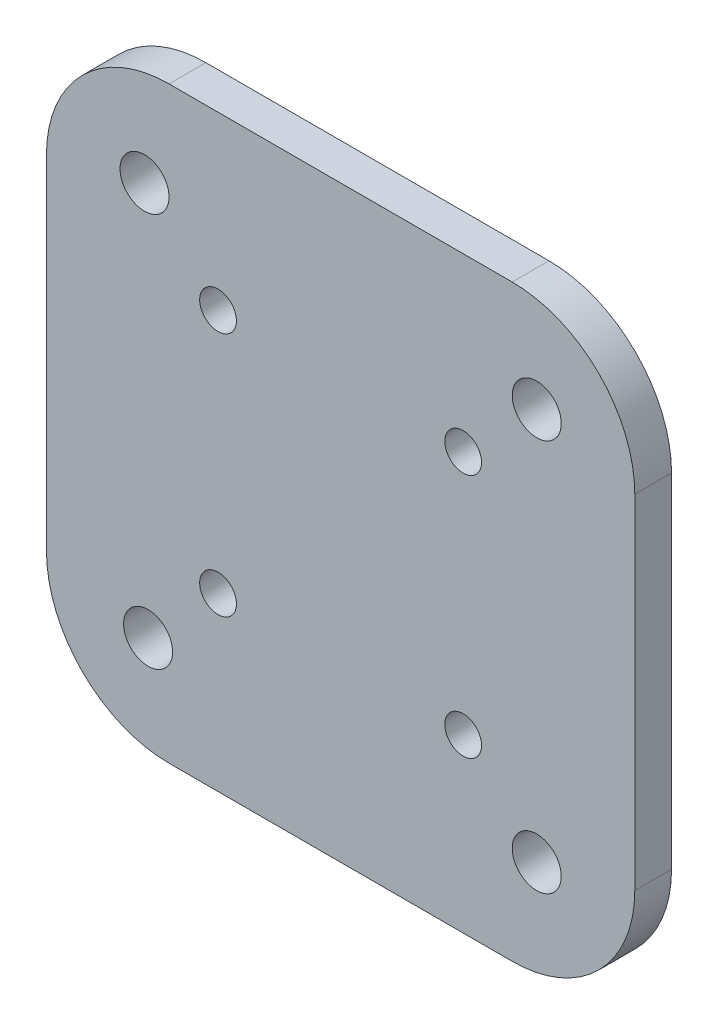
SolidWorks part; units mm, degrees
ref_plane "Front Plane" through (0, 0, 0) normal (0, 0, 1) x (1, 0, 0)
ref_plane "Top Plane" through (0, 0, 0) normal (0, 1, 0) x (1, 0, 0)
ref_plane "Right Plane" through (0, 0, 0) normal (1, 0, 0) x (0, 0, -1)
sketch "Sketch1" plane through (0, 0, 0) normal (0, 0, 1) x (1, 0, 0)
  line L5 (24, -24) -> (-24, -24)
  line L6 (24, -24) -> (24, 24)
  line L7 (24, 24) -> (-24, 24)
  line L8 (-24, -24) -> (-24, 24)
  line L9 (24, -24) -> (-24, 24) construction
  line L10 (24, 24) -> (-24, -24) construction
  line L11 (10, -10) -> (-10, -10) construction
  line L12 (10, -10) -> (10, 10) construction
  line L13 (10, 10) -> (-10, 10) construction
  line L14 (-10, -10) -> (-10, 10) construction
  line L15 (10, -10) -> (-10, 10) construction
  line L16 (10, 10) -> (-10, -10) construction
  line L17 (16, -16) -> (-16, -16) construction
  line L18 (16, -16) -> (16, 16) construction
  line L19 (16, 16) -> (-16, 16) construction
  line L20 (-16, -16) -> (-16, 16) construction
  line L21 (16, -16) -> (-16, 16) construction
  line L22 (16, 16) -> (-16, -16) construction
  circle A0 centre (10, 10) radius 1.5
  circle A1 centre (-10, 10) radius 1.5
  circle A2 centre (-10, -10) radius 1.5
  circle A3 centre (10, -10) radius 1.5
  circle A4 centre (-16, 16) radius 2
  circle A5 centre (16, 16) radius 2
  circle A6 centre (16, -16) radius 2
  circle A7 centre (-15.7084, -16) radius 2
  point P0 (0, 0)
  point P4 (0, 0)
  point P15 (0, 0)
  dimension "D5" = 3
  dimension "D6" = 3
  dimension "D7" = 3
  dimension "D8" = 3
  dimension "D1" = 48
  dimension "D2" = 48
  dimension "D3" = 20
  dimension "D4" = 20
  dimension "D9" = 32
  dimension "D10" = 32
extrude "Boss-Extrude1" add sketch "Sketch1" along normal blind 3
fillet "Fillet1" radius 10 1 edges at (-24, 24, 1.5)
fillet "Fillet2" radius 10 1 edges at (24, 24, 1.5)
fillet "Fillet3" radius 10 1 edges at (24, -24, 1.5)
fillet "Fillet4" radius 10 1 edges at (-24, -24, 1.5)
